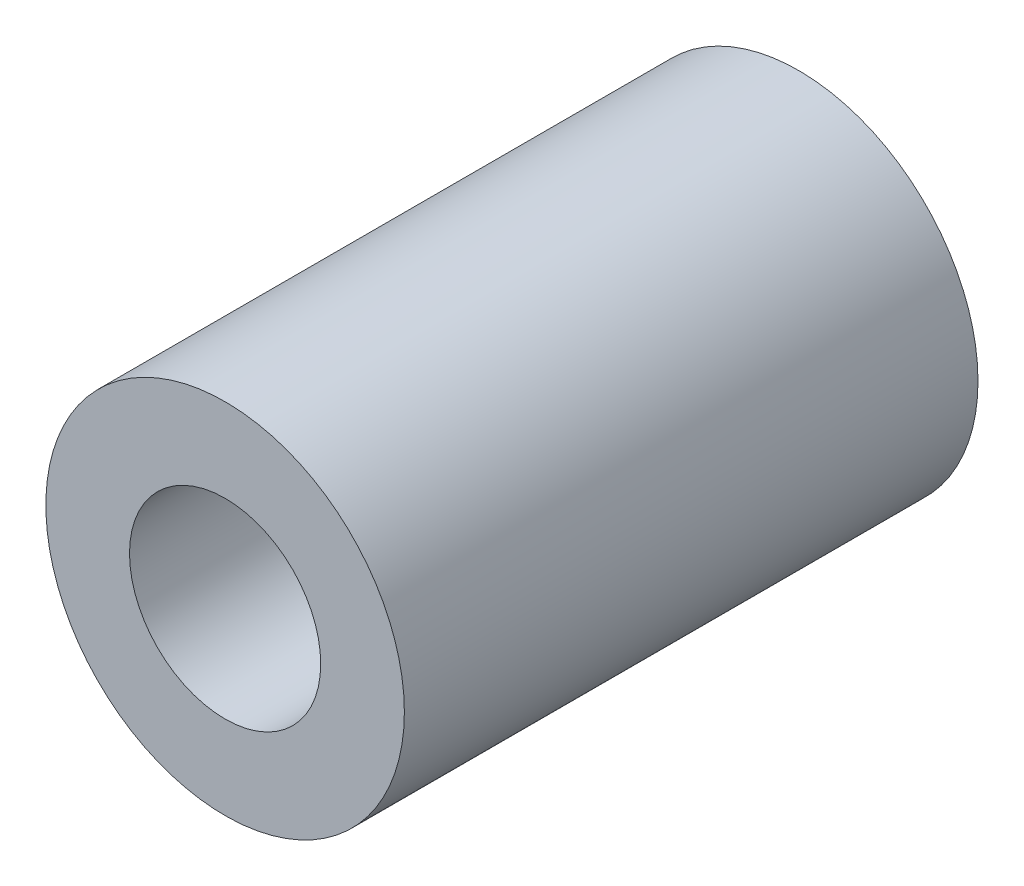
SolidWorks part; units mm, degrees
ref_plane "Front Plane" through (0, 0, 0) normal (0, 0, 1) x (1, 0, 0)
ref_plane "Top Plane" through (0, 0, 0) normal (0, 1, 0) x (1, 0, 0)
ref_plane "Right Plane" through (0, 0, 0) normal (1, 0, 0) x (0, 0, -1)
sketch "Sketch1" plane through (0, 0, 0) normal (0, 0, 1) x (1, 0, 0)
  circle A0 centre (0, 0) radius 7.5
  circle A1 centre (0, 0) radius 4
  dimension "D1" = 8
  dimension "D2" = 15
extrude "Boss-Extrude1" add sketch "Sketch1" along normal blind 24
